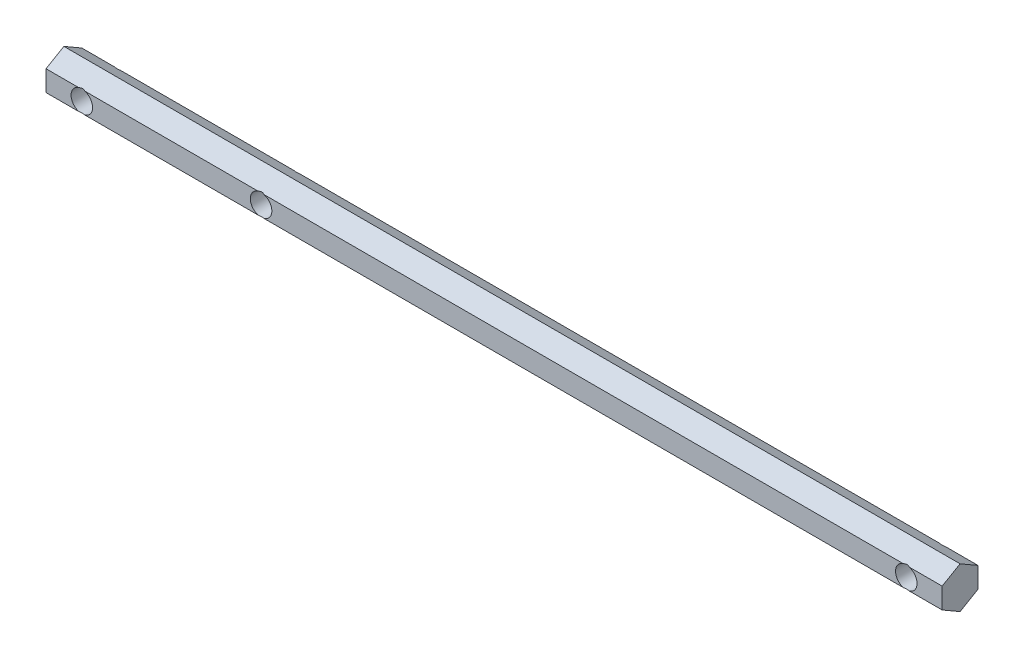
SolidWorks part; units mm, degrees
ref_plane "Plano frontal" through (0, 0, 0) normal (0, 0, 1) x (1, 0, 0)
ref_plane "Plano superior" through (0, 0, 0) normal (0, 1, 0) x (1, 0, 0)
ref_plane "Plano direito" through (0, 0, 0) normal (1, 0, 0) x (0, 0, -1)
sketch "Sketch1" plane through (0, 0, 0) normal (1, 0, 0) x (0, 0, -1)
  line L0 (-8.3414, 2.8868) -> (9.6861, 2.8868) construction
  line L1 (0, 5.7735) -> (-5, 2.8868)
  line L2 (-5, 2.8868) -> (-5, -2.8868)
  line L3 (-5, -2.8868) -> (0, -5.7735)
  line L4 (0, -5.7735) -> (5, -2.8868)
  line L5 (5, -2.8868) -> (5, 2.8868)
  line L6 (5, 2.8868) -> (0, 5.7735)
  line L7 (-8.3414, -2.8868) -> (9.6861, -2.8868) construction
  circle A0 centre (0, 0) radius 5 construction
  dimension "D1" = 10
extrude "Boss-Extrude1" add sketch "Sketch1" along normal mid plane 250
sketch "Sketch2" plane through (0, 0, 0) normal (0, 0, 1) x (1, 0, 0)
  line L0 (120.1463, 0) -> (-122.4896, 0) construction
  line L1 (0, 39.7277) -> (0, -43.0342) construction
  circle A0 centre (115, 0) radius 3
  circle A1 centre (-115, 0) radius 3
  circle A2 centre (-65, 0) radius 3
  dimension "D3" = 6
  dimension "D4" = 6
  dimension "D5" = 6
  dimension "D1" = 115
  dimension "D2" = 115
  dimension "D6" = 50
extrude "Cut-Extrude1" cut sketch "Sketch2" against normal through all both and the other way through all
